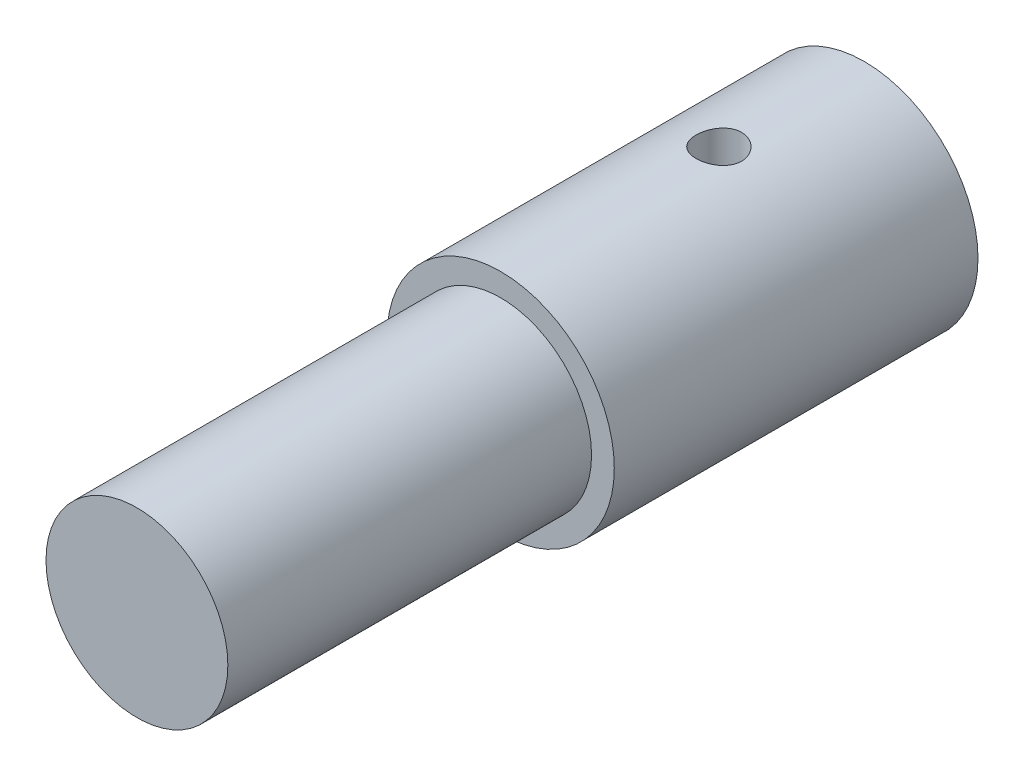
SolidWorks part; units mm, degrees
material "Plain Carbon Steel"
ref_plane "Front Plane" through (0, 0, 0) normal (0, 0, 1) x (1, 0, 0)
ref_plane "Top Plane" through (0, 0, 0) normal (0, 1, 0) x (1, 0, 0)
ref_plane "Right Plane" through (0, 0, 0) normal (1, 0, 0) x (0, 0, -1)
sketch "Sketch1" plane through (0, 0, 0) normal (0, 0, 1) x (1, 0, 0)
  circle A0 centre (0, 0) radius 3.175
  dimension "D1" = 6.35
extrude "Boss-Extrude1" add sketch "Sketch1" along normal blind 12.7
sketch "Sketch2" plane through (0, 0, 12.7) normal (0, 0, 1) x (1, 0, 0)
  line L0 (-6.35, 1.27) -> (6.35, 1.27)
  line L1 (0, -6.985) -> (0, 6.985) construction
  arc A0 (6.35, 1.27) -> (-6.35, 1.27) centre (0, 1.27) ccw
  circle A1 centre (0, 0) radius 3.175 construction
  dimension "D2" = 6.35
  dimension "D1" = 1.27
extrude "Cut-Extrude1" [suppressed] cut sketch "Sketch2" against normal blind 6.35
sketch "Sketch3" plane through (0, 0, 0) normal (0, 0, -1) x (-1, 0, 0)
  circle A0 centre (0, 0) radius 3.9688
  dimension "D1" = 7.9375
extrude "Boss-Extrude2" add sketch "Sketch3" along normal blind 12.7
sketch "Sketch4" plane through (0, 0, -12.7) normal (0, 0, -1) x (-1, 0, 0)
  circle A0 centre (0, 0) radius 1.5875
  dimension "D1" = 3.175
extrude "Cut-Extrude2" cut sketch "Sketch4" against normal blind 8.89
sketch "Sketch5" plane through (0, 0, 0) normal (0, 1, 0) x (1, 0, 0)
  line L1 (3.9688, 12.7) -> (-3.9688, 12.7) construction
  line L2 (0, -3.4925) -> (0, 3.4925) construction
  circle A0 centre (0, 7.62) radius 0.7937
  dimension "D1" = 1.5875
  dimension "D2" = 5.08
extrude "Cut-Extrude3" cut sketch "Sketch5" along normal through all
